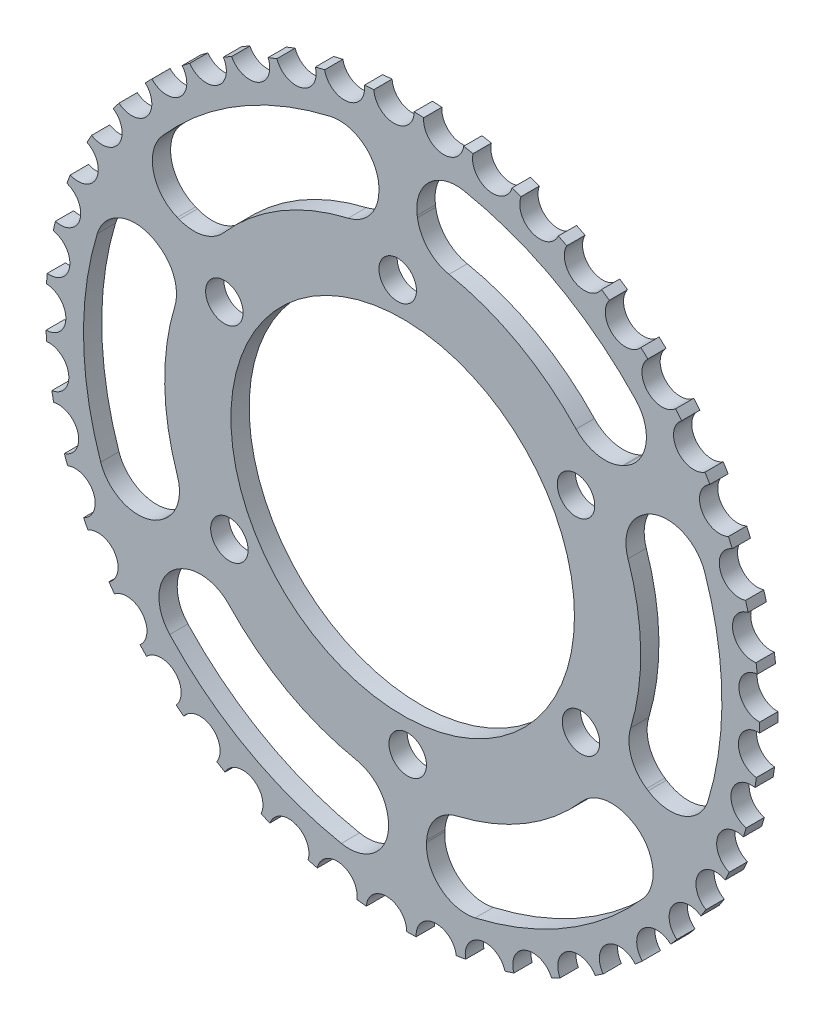
SolidWorks part; units mm, degrees
ref_plane "Front Plane" through (0, 0, 0) normal (0, 0, 1) x (1, 0, 0)
ref_plane "Top Plane" through (0, 0, 0) normal (0, 1, 0) x (1, 0, 0)
ref_plane "Right Plane" through (0, 0, 0) normal (1, 0, 0) x (0, 0, -1)
sketch "Sketch1" plane through (0, 0, 0) normal (0, 0, 1) x (1, 0, 0)
  circle A0 centre (0, 0) radius 114.3
extrude "Boss-Extrude1" add sketch "Sketch1" along normal blind 5.842
sketch "Sketch8" plane through (0, 0, 5.842) normal (0, 0, 1) x (1, 0, 0)
  line L1 (-1.6057, 89.6476) -> (-1.6057, 115.6059) construction
sketch "Sketch2" plane through (0, 0, 0) normal (0, 0, 1) x (1, 0, 0)
  circle A0 centre (0, 0) radius 54.9999
extrude "Cut-Extrude2" cut sketch "Sketch2" along normal through all
sketch "Sketch3" plane through (0, 0, 0) normal (0, 0, 1) x (1, 0, 0)
  line L0 (-1.6057, -199910.3524) -> (-1.6057, 200115.6059) construction
  circle A1 centre (-1.6057, 65.0001) radius 6
  circle A8 centre (55.4889, 33.8906) radius 6
  circle A9 centre (57.0946, -31.1095) radius 6
  circle A10 centre (1.6057, -65.0001) radius 6
  circle A11 centre (-55.4889, -33.8906) radius 6
  circle A12 centre (-57.0946, 31.1095) radius 6
  point P15 (0, 0)
  point P16 (0, 0)
  dimension "D1" = 6
extrude "Cut-Extrude3" cut sketch "Sketch3" along normal through all
sketch "Sketch5" plane through (0, 0, 5.842) normal (0, 0, 1) x (1, 0, 0)
  circle A0 centre (-2.7818, 114.2661) radius 6.4557
  circle A1 centre (0, 0) radius 114.3 construction
  circle A2 centre (13.148, 113.5413) radius 6.4557
  circle A3 centre (28.8219, 110.6064) radius 6.4557
  circle A4 centre (43.9349, 105.5188) radius 6.4557
  circle A5 centre (58.1927, 98.3773) radius 6.4557
  circle A6 centre (71.3178, 89.3211) radius 6.4557
  circle A7 centre (83.0549, 78.5263) radius 6.4557
  circle A8 centre (93.1753, 66.2031) radius 6.4557
  circle A9 centre (101.4822, 52.5913) radius 6.4557
  circle A10 centre (107.8139, 37.9559) radius 6.4557
  circle A11 centre (112.0471, 22.5817) radius 6.4557
  circle A12 centre (114.0994, 6.768) radius 6.4557
  circle A13 centre (113.931, -9.1775) radius 6.4557
  circle A14 centre (111.5449, -24.9443) radius 6.4557
  circle A15 centre (106.9878, -40.2256) radius 6.4557
  circle A16 centre (100.3483, -54.7239) radius 6.4557
  circle A17 centre (91.7556, -68.1571) radius 6.4557
  circle A18 centre (81.377, -80.2637) radius 6.4557
  circle A19 centre (69.4145, -90.8081) radius 6.4557
  circle A20 centre (56.1009, -99.585) radius 6.4557
  circle A21 centre (41.6954, -106.4236) radius 6.4557
  circle A22 centre (26.4783, -111.1908) radius 6.4557
  circle A23 centre (10.7459, -113.7937) radius 6.4557
  circle A24 centre (-5.1957, -114.1818) radius 6.4557
  circle A25 centre (-21.0362, -112.3475) radius 6.4557
  circle A26 centre (-36.4672, -108.3265) radius 6.4557
  circle A27 centre (-51.1885, -102.197) radius 6.4557
  circle A28 centre (-64.9134, -94.0784) radius 6.4557
  circle A29 centre (-77.3748, -84.1286) radius 6.4557
  circle A30 centre (-88.3303, -72.5414) radius 6.4557
  circle A31 centre (-97.5665, -59.5422) radius 6.4557
  circle A32 centre (-104.9036, -45.3841) radius 6.4557
  circle A33 centre (-110.199, -30.3427) radius 6.4557
  circle A34 centre (-113.3494, -14.7107) radius 6.4557
  circle A35 centre (-114.2936, 1.2077) radius 6.4557
  circle A36 centre (-113.0132, 17.1025) radius 6.4557
  circle A37 centre (-109.5332, 32.6645) radius 6.4557
  circle A38 centre (-103.9212, 47.5907) radius 6.4557
  circle A39 centre (-96.2865, 61.5906) radius 6.4557
  circle A40 centre (-86.7777, 74.3917) radius 6.4557
  circle A41 centre (-75.5799, 85.7448) radius 6.4557
  circle A42 centre (-62.911, 95.429) radius 6.4557
  circle A43 centre (-49.0176, 103.2558) radius 6.4557
  circle A44 centre (-34.1701, 109.0729) radius 6.4557
  circle A45 centre (-18.6575, 112.767) radius 6.4557
  point P95 (0, 0)
  dimension "D1" = 45
extrude "Cut-Extrude6" cut sketch "Sketch5" against normal blind 5.842
sketch "Sketch7" plane through (0, 0, 5.842) normal (0, 0, 1) x (1, 0, 0)
  line L4 (49.3046, 88.3451) -> (89.0378, 159.54) construction
  line L5 (6.1047, 75.9551) -> (2.2861, 102.1751)
  line L6 (61.44, 45.073) -> (85.0082, 56.7326)
  line L7 (68.8314, 32.6907) -> (89.6293, 49.1077)
  line L8 (69.7543, -30.6721) -> (91.636, -45.253)
  line L9 (62.7267, -43.2643) -> (87.3432, -53.0674)
  line L10 (8.3144, -75.745) -> (6.6278, -101.9856)
  line L11 (-6.1047, -75.9551) -> (-2.2861, -102.1751)
  line L12 (-61.44, -45.073) -> (-85.0082, -56.7326)
  line L13 (-68.8314, -32.6907) -> (-89.6293, -49.1077)
  line L14 (-69.7543, 30.6721) -> (-91.636, 45.253)
  line L15 (-62.7267, 43.2643) -> (-87.3432, 53.0674)
  line L16 (-8.3144, 75.745) -> (-6.6278, 101.9856)
  arc A0 (2.2861, 102.1751) -> (85.0082, 56.7326) centre (0, 0) cw
  arc A1 (6.1047, 75.9551) -> (61.44, 45.073) centre (0, 0) cw
  arc A2 (89.6293, 49.1077) -> (91.636, -45.253) centre (0, 0) cw
  arc A3 (68.8314, 32.6907) -> (69.7543, -30.6721) centre (0, 0) cw
  arc A4 (87.3432, -53.0674) -> (6.6278, -101.9856) centre (0, 0) cw
  arc A5 (62.7267, -43.2643) -> (8.3144, -75.745) centre (0, 0) cw
  arc A6 (-2.2861, -102.1751) -> (-85.0082, -56.7326) centre (0, 0) cw
  arc A7 (-6.1047, -75.9551) -> (-61.44, -45.073) centre (0, 0) cw
  arc A8 (-89.6293, -49.1077) -> (-91.636, 45.253) centre (0, 0) cw
  arc A9 (-68.8314, -32.6907) -> (-69.7543, 30.6721) centre (0, 0) cw
  arc A10 (-87.3432, 53.0674) -> (-6.6278, 101.9856) centre (0, 0) cw
  arc A11 (-62.7267, 43.2643) -> (-8.3144, 75.745) centre (0, 0) cw
  point P8 (37.1348, 66.539)
  point P32 (0, 0)
  dimension "D1" = 6
extrude "Cut-Extrude7" cut sketch "Sketch7" against normal blind 5.842
fillet "Fillet2" radius 12.7 24 edges at (91.636, -45.253, 2.921) (89.6293, 49.1077, 2.921) (68.8314, 32.6907, 2.921) (69.7543, -30.6721, 2.921) (61.44, 45.073, 2.921) (-85.0082, -56.7326, 2.921) (-89.6293, -49.1077, 2.921) (-69.7543, 30.6721, 2.921) (-62.7267, 43.2643, 2.921) (6.1047, 75.9551, 2.921) (-8.3144, 75.745, 2.921) (6.6278, -101.9856, 2.921) (8.3144, -75.745, 2.921) (62.7267, -43.2643, 2.921) (87.3432, -53.0674, 2.921) (-61.44, -45.073, 2.921) (-6.1047, -75.9551, 2.921) (-2.2861, -102.1751, 2.921) (-68.8314, -32.6907, 2.921) (-91.636, 45.253, 2.921) (85.0082, 56.7326, 2.921) (2.2861, 102.1751, 2.921) (-6.6278, 101.9856, 2.921) (-87.3432, 53.0674, 2.921)
sketch "Sketch9" plane through (0, 0, 5.842) normal (0, 0, 1) x (1, 0, 0)
  line L0 (111.9857, 0) -> (111.9857, 23.29)
  line L1 (111.9857, 0) -> (120.9946, 24.7517)
  dimension "D1" = 20
